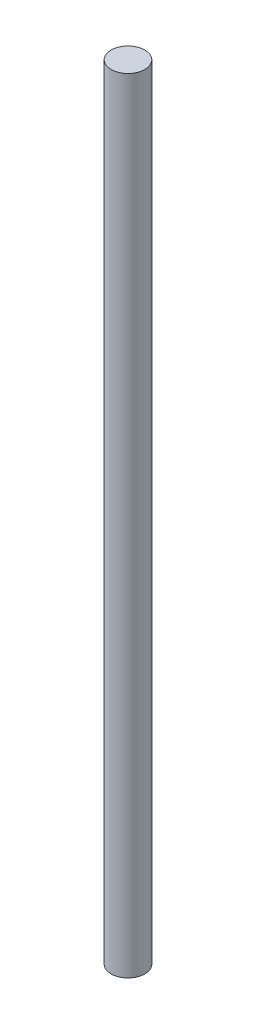
SolidWorks part; units mm, degrees
material "1060-H12"
ref_plane "Alzado" through (0, 0, 0) normal (0, 0, 1) x (1, 0, 0)
ref_plane "Planta" through (0, 0, 0) normal (0, 1, 0) x (1, 0, 0)
ref_plane "Vista lateral" through (0, 0, 0) normal (1, 0, 0) x (0, 0, -1)
sketch "Croquis1" plane through (0, 0, 0) normal (0, 1, 0) x (1, 0, 0)
  circle A0 centre (0, 0) radius 4
  dimension "D1" = 8
extrude "Saliente-Extruir1" add sketch "Croquis1" along normal blind 186
